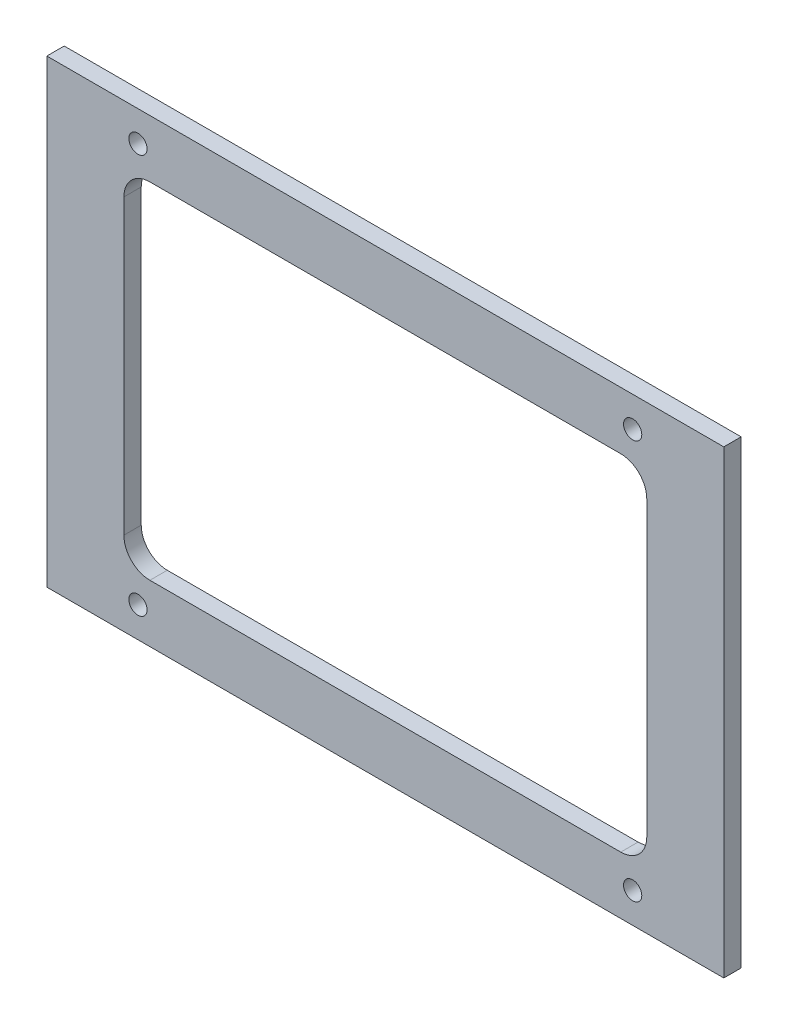
SolidWorks part; units mm, degrees
ref_plane "Front Plane" through (0, 0, 0) normal (0, 0, 1) x (1, 0, 0)
ref_plane "Top Plane" through (0, 0, 0) normal (0, 1, 0) x (1, 0, 0)
ref_plane "Right Plane" through (0, 0, 0) normal (1, 0, 0) x (0, 0, -1)
sketch "Sketch1" plane through (0, 0, 0) normal (0, 0, 1) x (1, 0, 0)
  line L1 (-78, 53) -> (78, 53)
  line L2 (-78, 53) -> (-78, -53)
  line L3 (-78, -53) -> (78, -53)
  line L4 (78, 53) -> (78, -53)
  line L5 (-78, 53) -> (78, -53) construction
  line L6 (-78, -53) -> (78, 53) construction
  point P0 (0, 0)
  dimension "D1" = 156
  dimension "D2" = 106
extrude "Boss-Extrude1" add sketch "Sketch1" against normal blind 4
sketch "Sketch2" plane through (0, 0, 0) normal (0, 0, 1) x (1, 0, 0)
  line L0 (0, 53) -> (0, -53) construction
  line L1 (78, 53) -> (-78, 53) construction
  line L2 (-78, -53) -> (78, -53) construction
  line L3 (-57, 46) -> (57, 46)
  line L4 (-57, 46) -> (-57, -46)
  line L5 (-57, -46) -> (57, -46)
  line L6 (57, 46) -> (57, -46)
  line L7 (-57, 46) -> (57, -46) construction
  line L8 (-57, -46) -> (57, 46) construction
  line L9 (-54.25, 39.75) -> (54.25, 39.75)
  line L10 (-60.25, 33.75) -> (-60.25, -33.75)
  line L11 (-54.25, -39.75) -> (54.25, -39.75)
  line L12 (60.25, 33.75) -> (60.25, -33.75)
  line L13 (-60.25, 39.75) -> (60.25, -39.75) construction
  line L14 (-60.25, -39.75) -> (60.25, 39.75) construction
  circle A0 centre (-57, 46) radius 2.1
  circle A1 centre (57, 46) radius 2.1
  circle A2 centre (-57, -46) radius 2.1
  circle A3 centre (57, -46) radius 2.1
  arc A4 (54.25, -39.75) -> (60.25, -33.75) centre (54.25, -33.75) ccw
  arc A5 (-60.25, -33.75) -> (-54.25, -39.75) centre (-54.25, -33.75) ccw
  arc A6 (54.25, 39.75) -> (60.25, 33.75) centre (54.25, 33.75) cw
  arc A7 (-54.25, 39.75) -> (-60.25, 33.75) centre (-54.25, 33.75) ccw
  point P6 (0, 0)
  point P15 (0, 0)
  dimension "D3" = 4.2
  dimension "D4" = 6
  dimension "D1" = 114
  dimension "D2" = 92
extrude "Cut-Extrude1" cut sketch "Sketch2" against normal up to next contours A6 L6 A4 L12 | L9 A7 L4 A5 L11 A4 L6 A6 | L4 A7 L10 A5 | L6 A1 L3 | L3 A1 L6 | L3 A0 L4 | L4 A0 L3 | L5 A2 L4 | L4 A2 L5 | L6 A3 L5 | L5 A3 L6
